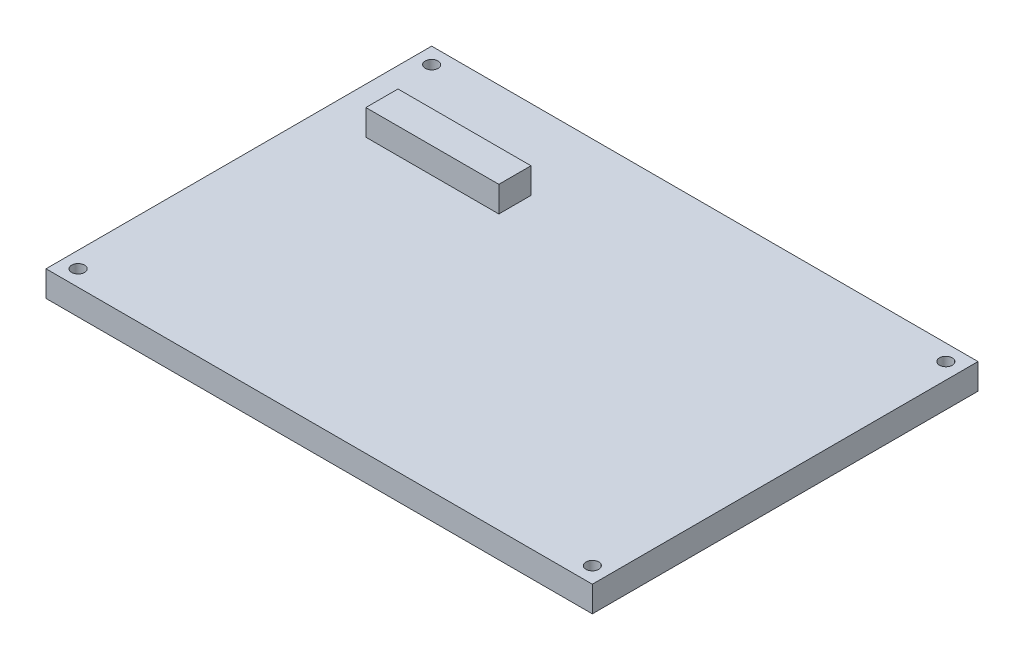
SolidWorks part; units mm, degrees
ref_plane "Front Plane" through (0, 0, 0) normal (0, 0, 1) x (1, 0, 0)
ref_plane "Top Plane" through (0, 0, 0) normal (0, 1, 0) x (1, 0, 0)
ref_plane "Right Plane" through (0, 0, 0) normal (1, 0, 0) x (0, 0, -1)
sketch "Sketch1" plane through (0, 0, 0) normal (0, 1, 0) x (1, 0, 0)
  line L1 (85, -60) -> (-85, -60)
  line L2 (85, -60) -> (85, 60)
  line L3 (85, 60) -> (-85, 60)
  line L4 (-85, -60) -> (-85, 60)
  line L5 (85, -60) -> (-85, 60) construction
  line L6 (85, 60) -> (-85, -60) construction
  point P0 (0, 0)
  dimension "D1" = 170
  dimension "D2" = 120
extrude "Boss-Extrude1" add sketch "Sketch1" along normal blind 8 contours L2 L1 L4 L3
sketch "Sketch2" plane through (-17.7915, 8, -1.3749) normal (0, 1, 0) x (1, 0, 0)
  line L1 (-52.8988, 33.84) -> (-11.5182, 33.84)
  line L2 (-52.8988, 33.84) -> (-52.8988, 23.84)
  line L3 (-52.8988, 23.84) -> (-11.5182, 23.84)
  line L4 (-11.5182, 33.84) -> (-11.5182, 23.84)
  line L5 (-52.8988, 33.84) -> (-11.5182, 23.84) construction
  line L6 (-52.8988, 23.84) -> (-11.5182, 33.84) construction
  line L7 (-67.2085, -61.3749) -> (-67.2085, 58.6251) construction
  point P0 (-32.2085, 28.84)
  point P7 (0, 0)
  dimension "D1" = 10
  dimension "D2" = 35
extrude "Boss-Extrude2" add sketch "Sketch2" along normal blind 8 contours L2 L1 L4 L3
sketch "Sketch3" plane through (0, 8, 0) normal (0, 1, 0) x (1, 0, 0)
  line L0 (-85, -60) -> (-85, 60) construction
  line L1 (85, 60) -> (-85, 60) construction
  line L2 (85, -60) -> (-85, -60) construction
  line L3 (85, -60) -> (85, 60) construction
  circle A0 centre (-80, 55) radius 2
  circle A1 centre (-80, -55) radius 2
  circle A2 centre (80, 55) radius 2
  circle A3 centre (80, -55) radius 2
  dimension "D1" = 5
  dimension "D3" = 5
  dimension "D7" = 5
  dimension "D2" = 5
  dimension "D4" = 5
  dimension "D5" = 5
  dimension "D6" = 5
  dimension "D8" = 5
extrude "Cut-Extrude1" cut sketch "Sketch3" against normal blind 8
